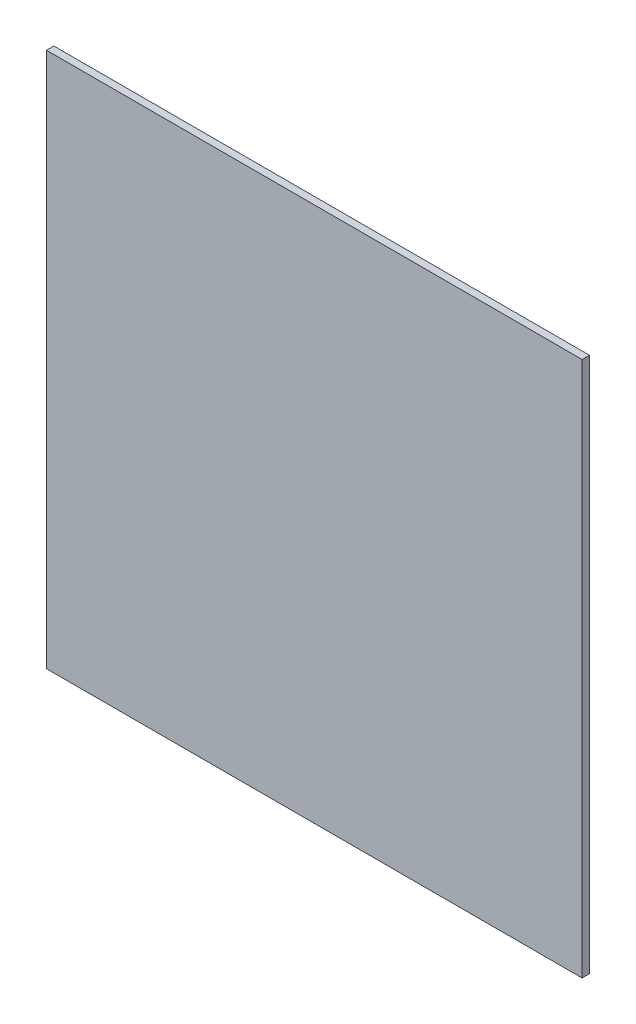
SolidWorks part; units mm, degrees
ref_plane "前视基准面" through (0, 0, 0) normal (0, 0, 1) x (1, 0, 0)
ref_plane "上视基准面" through (0, 0, 0) normal (0, 1, 0) x (1, 0, 0)
ref_plane "右视基准面" through (0, 0, 0) normal (1, 0, 0) x (0, 0, -1)
sketch "草图1" plane through (0, 0, 0) normal (0, 0, 1) x (1, 0, 0)
  line L1 (0, 0) -> (200, 0)
  line L2 (0, 0) -> (0, 200)
  line L3 (0, 200) -> (200, 200)
  line L4 (200, 0) -> (200, 200)
extrude "凸台-拉伸1" add sketch "草图1" along normal blind 2.75
